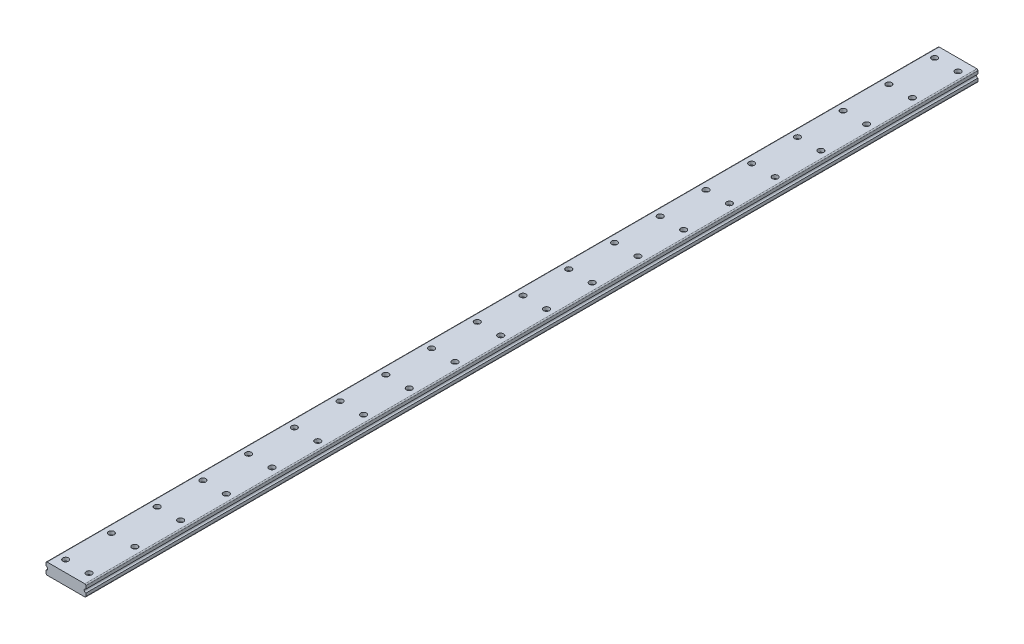
SolidWorks part; units mm, degrees
ref_plane "Front Plane" through (0, 0, 0) normal (0, 0, 1) x (1, 0, 0)
ref_plane "Top Plane" through (0, 0, 0) normal (0, 1, 0) x (1, 0, 0)
ref_plane "Right Plane" through (0, 0, 0) normal (1, 0, 0) x (0, 0, -1)
sketch "Sketch1" plane through (0, 0, 0) normal (0, 0, 1) x (1, 0, 0)
  line L0 (0, 13) -> (0, 18)
  line L1 (2, 0) -> (67.85, 0)
  line L2 (0, 2) -> (0, 7)
  line L3 (2, 20) -> (67.85, 20)
  line L4 (69.85, 2) -> (69.85, 7)
  line L5 (69.85, 13) -> (69.85, 18)
  arc A0 (2, 0) -> (0, 2) centre (2, 2) cw
  arc A1 (67.85, 0) -> (69.85, 2) centre (67.85, 2) ccw
  arc A2 (67.85, 20) -> (69.85, 18) centre (67.85, 18) cw
  arc A3 (2, 20) -> (0, 18) centre (2, 18) ccw
  arc A4 (0, 7) -> (0, 13) centre (0, 10) ccw
  arc A5 (69.85, 7) -> (69.85, 13) centre (69.85, 10) cw
  point P7 (0, 0)
  point P10 (69.85, 0)
  point P13 (69.85, 20)
  point P22 (0, 0)
  dimension "D3" = 2
  dimension "D4" = 3
  dimension "D1" = 69.85
  dimension "D2" = 20
  dimension "D5" = 10
extrude "Boss-Extrude1" add sketch "Sketch1" along normal blind 1560.45
sketch "Sketch2" plane through (0, 20, 0) normal (0, 1, 0) x (1, 0, 0)
  line L0 (67.85, -1560.45) -> (2, -1560.45) construction
  circle A0 centre (14.425, -1540.45) radius 5.05
  circle A1 centre (55.425, -1540.45) radius 5.05
  point P7 (34.925, -1560.45)
  dimension "D2" = 10.1
  dimension "D1" = 20
  dimension "D3" = 41
  dimension "D4" = 20.5
extrude "Cut-Extrude1" cut sketch "Sketch2" against normal blind 6
pattern_linear "LPattern1" count 20 spacing 80 along (0, 0, -1) of "Cut-Extrude1"
